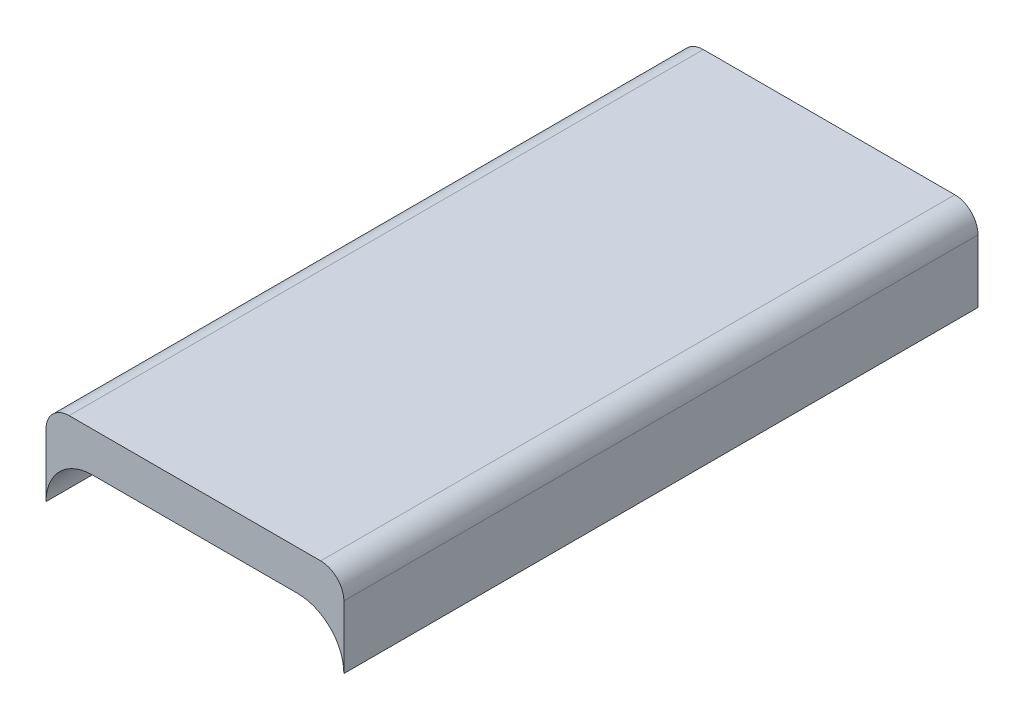
SolidWorks part; units mm, degrees
ref_plane "Front Plane" through (0, 0, 0) normal (0, 0, 1) x (1, 0, 0)
ref_plane "Top Plane" through (0, 0, 0) normal (0, 1, 0) x (1, 0, 0)
ref_plane "Right Plane" through (0, 0, 0) normal (1, 0, 0) x (0, 0, -1)
sketch "Sketch1" plane through (0, 0, 0) normal (0, 1, 0) x (1, 0, 0)
  line L0 (22.5, 47.9) -> (-22.5, -47.9) construction
  line L1 (-22.5, 47.9) -> (22.5, 47.9)
  line L2 (-22.5, 47.9) -> (-22.5, -47.9)
  line L3 (-22.5, -47.9) -> (22.5, -47.9)
  line L4 (22.5, 47.9) -> (22.5, -47.9)
  line L5 (-22.5, 47.9) -> (22.5, -47.9) construction
  point P4 (0, 0)
  point P5 (0, 0)
  dimension "D1" = 95.8
  dimension "D2" = 45
extrude "Boss-Extrude1" add sketch "Sketch1" along normal blind 13
sketch "Sketch15" plane through (0, 0, 47.9) normal (0, 0, 1) x (1, 0, 0)
  line L0 (-15.5, 7) -> (15.5, 7)
  line L1 (0, 0) -> (0, 7) construction
  line L2 (-15.5, 0) -> (-22.5, 0) construction
  line L3 (-22.5, 0) -> (22.5, 0) construction
  line L4 (-22.5, 0) -> (22.5, 0)
  line L7 (-15.5, 0) -> (-20.4497, 4.9497) construction
  arc A0 (-15.5, 7) -> (-22.5, 0) centre (-15.5, 0) ccw
  arc A1 (15.5, 7) -> (22.5, 0) centre (15.5, 0) cw
  dimension "D1" = 7
extrude "Cut-Extrude1" cut sketch "Sketch15" against normal through all
fillet "Fillet2" radius 3.5 2 edges at (-22.5, 13, 0) (22.5, 13, 0)
